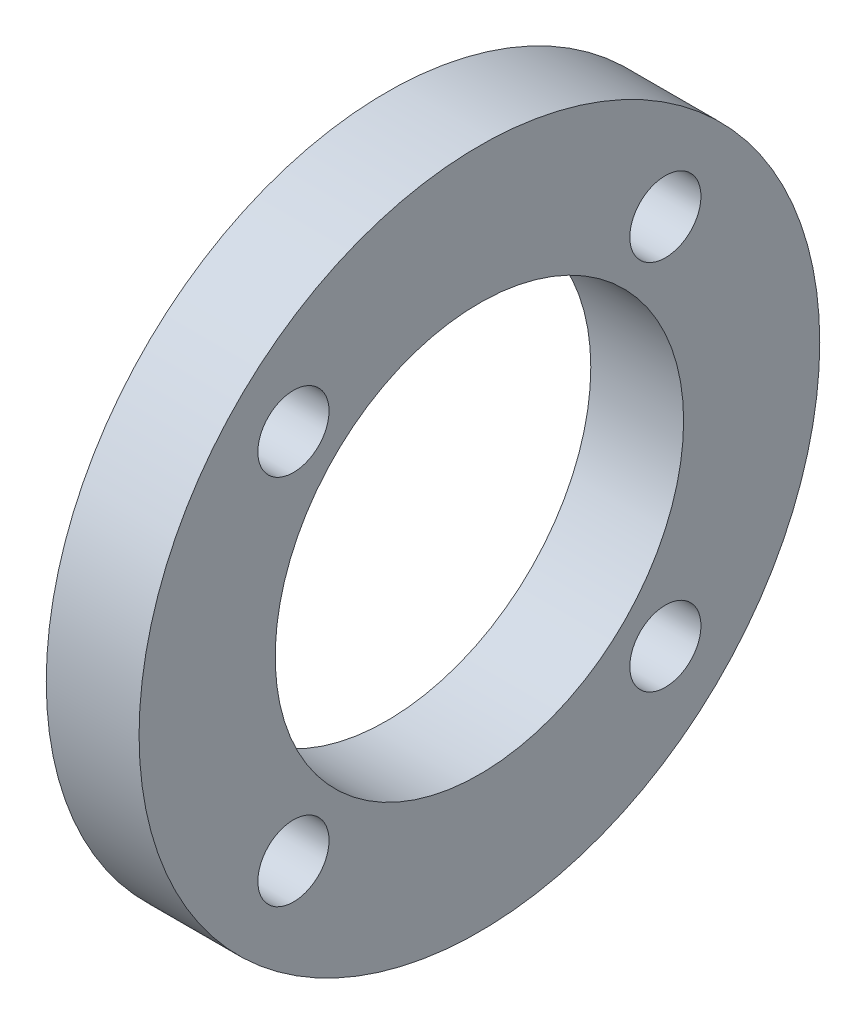
SolidWorks part; units mm, degrees
material "Alumina"
ref_plane "Front Plane" through (0, 0, 0) normal (0, 0, 1) x (1, 0, 0)
ref_plane "Top Plane" through (0, 0, 0) normal (0, 1, 0) x (1, 0, 0)
ref_plane "Right Plane" through (0, 0, 0) normal (1, 0, 0) x (0, 0, -1)
sketch "Sketch2" plane through (0, 0, 0) normal (1, 0, 0) x (0, 0, -1)
  circle A0 centre (0, 0) radius 11
  circle A1 centre (0, 0) radius 6.6
  dimension "D1" = 22
  dimension "D2" = 13.2
extrude "Boss-Extrude1" add sketch "Sketch2" along normal blind 3 separate body
sketch "Sketch3" plane through (0, 0, 0) normal (1, 0, 0) x (0, 0, -1)
  line L0 (0, 0) -> (11, 0) construction
  line L1 (0, 0) -> (0, 11) construction
  line L2 (0, 0) -> (7.7782, 7.7782) construction
  circle A0 centre (0, 0) radius 11 construction
  circle A1 centre (0, 0) radius 8.5 construction
  circle A2 centre (6.0104, 6.0104) radius 1.15
  circle A3 centre (6.0104, -6.0104) radius 1.15
  circle A4 centre (-6.0104, -6.0104) radius 1.15
  circle A5 centre (-6.0104, 6.0104) radius 1.15
  point P20 (0, 0)
  dimension "D1" = 17
  dimension "D3" = 2.3
  dimension "D2" = 45
  dimension "D4" = 4
extrude "Cut-Extrude1" cut sketch "Sketch3" along normal through all
